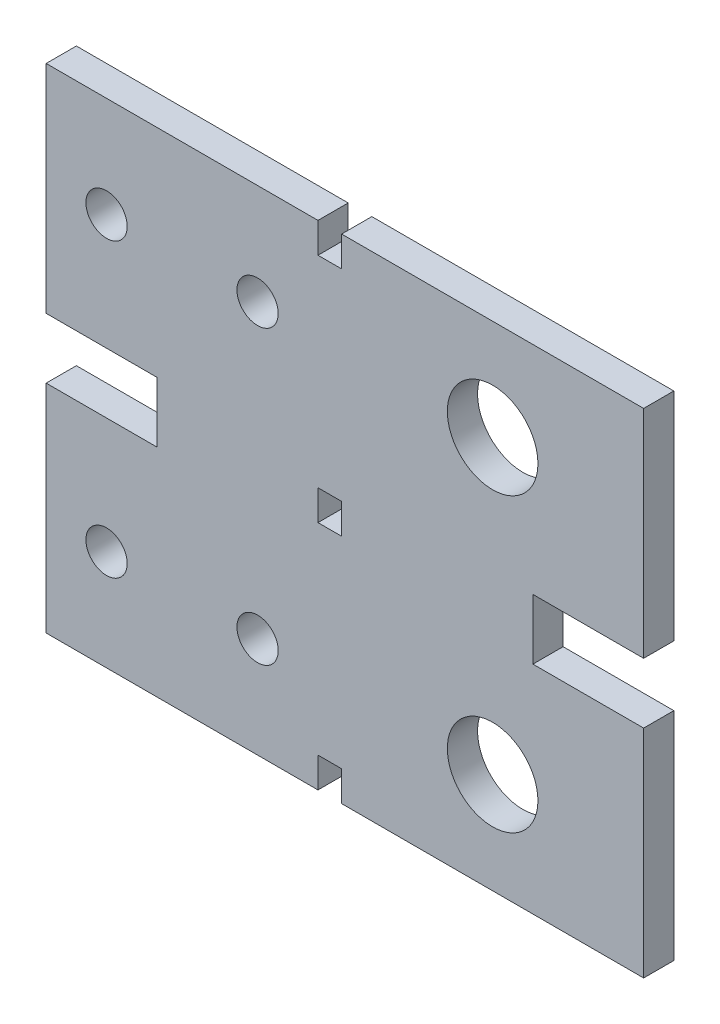
SolidWorks part; units mm, degrees
ref_plane "Front Plane" through (0, 0, 0) normal (0, 0, 1) x (1, 0, 0)
ref_plane "Top Plane" through (0, 0, 0) normal (0, 1, 0) x (1, 0, 0)
ref_plane "Right Plane" through (0, 0, 0) normal (1, 0, 0) x (0, 0, -1)
sketch "Sketch2" plane through (0, 0, 0) normal (0, 0, 1) x (1, 0, 0)
  line L1 (0, 0) -> (27, 0)
  line L2 (0, 0) -> (0, 49)
  line L3 (0, 49) -> (27, 49)
  line L4 (27, 0) -> (27, 49)
  line L5 (6, 39) -> (21, 39) construction
  line L6 (6, 39) -> (6, 10) construction
  line L7 (6, 10) -> (21, 10) construction
  line L8 (21, 39) -> (21, 10) construction
  circle A0 centre (6, 39) radius 2.05
  circle A1 centre (21, 39) radius 2.05
  circle A2 centre (6, 10) radius 2.05
  circle A3 centre (21, 10) radius 2.05
  point P13 (13.5, 10)
  point P14 (13.5, 0)
  point P15 (6, 24.5)
  point P16 (0, 24.5)
  dimension "D1" = 4.1
  dimension "D2" = 15
  dimension "D3" = 29
  dimension "D4" = 10
  dimension "D5" = 6
extrude "Boss-Extrude1" add sketch "Sketch2" along normal blind 3
sketch "Sketch8" plane through (0, 0, 3) normal (0, 0, 1) x (1, 0, 0)
  line L0 (27, 49) -> (0, 49) construction
  line L1 (29.35, 0) -> (59.35, 0)
  line L2 (29.35, 0) -> (29.35, 3)
  line L3 (29.35, 49) -> (59.35, 49)
  line L4 (59.35, 0) -> (59.35, 49)
  line L5 (0, 0) -> (27, 0) construction
  line L6 (27, 0) -> (27, 49) construction
  line L7 (29.35, 46) -> (29.35, 49)
  line L8 (27, 46) -> (29.35, 46)
  line L10 (27, 26) -> (29.35, 26)
  line L12 (27, 23) -> (29.35, 23)
  line L14 (27, 3) -> (29.35, 3)
  line L16 (29.35, 23) -> (29.35, 26)
  line L17 (27, 46) -> (27, 26)
  line L18 (27, 23) -> (27, 3)
  circle A0 centre (44.35, 39) radius 4.5
  circle A1 centre (44.35, 10) radius 4.5
  point P15 (59.35, 24.5)
  dimension "D2" = 9
  dimension "D3" = 15
  dimension "D4" = 29
  dimension "D6" = 14.5
  dimension "D1" = 2.35
  dimension "D5" = 30
  dimension "D7" = 20
  dimension "D8" = 3
extrude "Boss-Extrude3" add sketch "Sketch8" against normal up to surface (3 mm away) up to face at (8.05, 10, 0)
sketch "Sketch9" plane through (0, 0, 3) normal (0, 0, 1) x (1, 0, 0)
  line L0 (0, 49) -> (0, 0) construction
  line L1 (0, 27.5) -> (11, 27.5)
  line L2 (0, 27.5) -> (0, 21.5)
  line L3 (0, 21.5) -> (11, 21.5)
  line L4 (11, 27.5) -> (11, 21.5)
  line L5 (59.35, 0) -> (59.35, 49) construction
  line L6 (59.35, 27.5) -> (48.35, 27.5)
  line L7 (59.35, 27.5) -> (59.35, 21.5)
  line L8 (59.35, 21.5) -> (48.35, 21.5)
  line L9 (48.35, 27.5) -> (48.35, 21.5)
  point P12 (59.35, 24.5)
  point P13 (59.35, 24.5)
  point P14 (0, 24.5)
  point P15 (0, 24.5)
  dimension "D1" = 6
  dimension "D2" = 11
extrude "Cut-Extrude4" cut sketch "Sketch9" against normal through all
